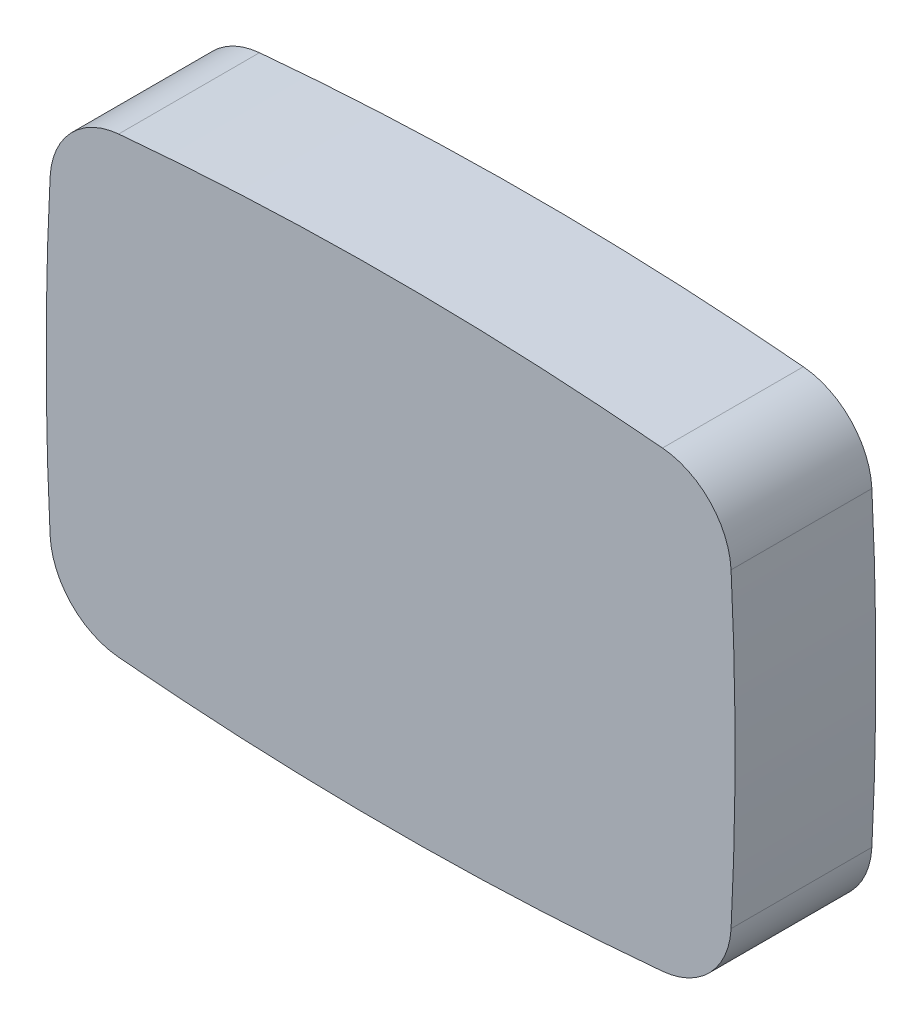
SolidWorks part; units mm, degrees
material "AW5083 AlMg4,5Mn"
ref_plane "Ebene vorne" through (0, 0, 0) normal (0, 0, 1) x (1, 0, 0)
ref_plane "Ebene oben" through (0, 0, 0) normal (0, 1, 0) x (1, 0, 0)
ref_plane "Ebene rechts" through (0, 0, 0) normal (1, 0, 0) x (0, 0, -1)
sketch "Skizze2" plane through (0, 0, 0) normal (0, 0, 1) x (1, 0, 0)
  line L1 (-68.5, 47.5) -> (68.5, 47.5) construction
  line L2 (-68.5, 47.5) -> (-68.5, -47.5) construction
  line L3 (-68.5, -47.5) -> (68.5, -47.5) construction
  line L4 (68.5, 47.5) -> (68.5, -47.5) construction
  line L5 (0, -47.5) -> (0, 47.5) construction
  line L6 (-68.5, 0) -> (68.5, 0) construction
  arc A0 (54.076, 45.0582) -> (-54.076, 45.0582) centre (0, -552.5) ccw
  arc A1 (-67.7042, 30.8915) -> (-67.7042, -30.8915) centre (531.5, 0) ccw
  arc A2 (-54.076, 45.0582) -> (-67.7042, 30.8915) centre (-52.7241, 30.1192) ccw
  arc A3 (67.7042, 30.8915) -> (67.7042, -30.8915) centre (-531.5, 0) cw
  arc A4 (54.076, 45.0582) -> (67.7042, 30.8915) centre (52.7241, 30.1192) cw
  arc A5 (54.076, -45.0582) -> (67.7042, -30.8915) centre (52.7241, -30.1192) ccw
  arc A6 (54.076, -45.0582) -> (-54.076, -45.0582) centre (0, 552.5) cw
  arc A7 (-54.076, -45.0582) -> (-67.7042, -30.8915) centre (-52.7241, -30.1192) cw
  point P0 (0, 0)
  dimension "D3" = 600
  dimension "D4" = 600
  dimension "D5" = 15
  dimension "D1" = 137
  dimension "D2" = 95
extrude "Grundform" add sketch "Skizze2" along normal blind 28
sketch "Mittellinien" plane through (0, 0, 0) normal (0, 0, -1) x (-1, 0, 0)
  line L0 (-63.5342, 40.5184) -> (0, 0) construction
  line L1 (0, 0) -> (-68.5, 0) construction
  line L2 (0, 0) -> (63.5342, -40.5184) construction
  line L3 (0, 0) -> (-63.5342, -40.5184) construction
  line L4 (63.5342, 40.5184) -> (0, 0) construction
  arc A0 (-67.7042, 30.8915) -> (-67.7042, -30.8915) centre (531.5, 0) ccw construction
  arc A1 (-67.7042, -30.8915) -> (-54.076, -45.0582) centre (-52.7241, -30.1192) ccw construction
  arc A2 (-54.076, 45.0582) -> (-67.7042, 30.8915) centre (-52.7241, 30.1192) ccw construction
  arc A3 (54.076, -45.0582) -> (67.7042, -30.8915) centre (52.7241, -30.1192) ccw construction
  arc A4 (67.7042, 30.8915) -> (54.076, 45.0582) centre (52.7241, 30.1192) ccw construction
  dimension "D1" = 68.5
  dimension "D4" = 75.3547
  dimension "D8" = 32.527
sketch "Radius lang 1" plane through (0, 0, 0) normal (0, 1, 0) x (1, 0, 0)
  line L0 (-54.076, -28) -> (54.076, -28) construction
  line L2 (0, 0) -> (0, 20)
  line L3 (54.076, 0) -> (-54.076, 0) construction
  line L4 (68.5, 0) -> (0, 0)
  arc A0 (68.5, 0) -> (0, 20) centre (0, -107.3063) ccw
  dimension "D1" = 48
  dimension "D2" = 127.3063
sketch "Seite 2" plane through (0, 0, 0) normal (1, 0, 0) x (0, 0, -1)
  line L0 (0, 0) -> (0, -47.5)
  line L1 (20, 0) -> (0, 0)
  arc A1 (17.8273, -16) -> (20, 0) centre (-40, 0) ccw
  arc A2 (0, -47.5) -> (17.8273, -16) centre (-54.0615, 3.8906) ccw
  dimension "D1" = 60
  dimension "D4" = 74.5899
  dimension "D2" = 20
  dimension "D3" = 16
ref_plane "Ebene2" through (0, -14.0128, -19.2722) normal (0, -0.5881, -0.8088) x (-1, 0, 0)
sketch "Schraeg1" plane through (0, -14.0128, -19.2722) normal (0, -0.5881, -0.8088) x (-1, 0, 0)
  line L1 (0, -32.7714) -> (63.5342, -32.7714)
  line L2 (0, -2.4569) -> (0, -32.7714)
  line L3 (0, -32.7714) -> (-63.5342, -32.7714) construction
  arc A0 (0, -2.4569) -> (63.5342, -32.7714) centre (0, -84.1928) cw
  arc A1 (0, -2.4569) -> (-63.5342, -32.7714) centre (0, -84.1928) ccw construction
sketch "Radius lang 2" plane through (0, 0, 0) normal (0, 1, 0) x (1, 0, 0)
  line L0 (0, 0) -> (0, 20) construction
  line L1 (0, 0) -> (0, 20)
  line L2 (-68.5, 0) -> (0, 0)
  arc A0 (0, 20) -> (-68.5, 0) centre (0, -107.3063) ccw
  arc A1 (68.5, 0) -> (0, 20) centre (0, -107.3063) ccw construction
sketch "Skizze36" plane through (0, 0, 0) normal (1, 0, 0) x (0, 0, -1)
  line L0 (0, 0) -> (20, 0) construction
  line L1 (0, 0) -> (20, 0)
  line L2 (0, 40.5184) -> (0, 0) construction
  line L3 (0, 47.5) -> (0, 0)
  arc A0 (20, 0) -> (17.8273, 16) centre (-40, 0) ccw
  arc A1 (17.8273, -16) -> (20, 0) centre (-40, 0) ccw construction
  arc A2 (17.8273, 16) -> (0, 47.5) centre (-54.0615, -3.8906) ccw
  arc A3 (0, -47.5) -> (17.8273, -16) centre (-54.0615, 3.8906) ccw construction
ref_plane "Ebene3" through (0, 14.0128, -19.2722) normal (0, 0.5881, -0.8088) x (-1, 0, 0)
sketch "Scharaeg2" plane through (0, 14.0128, -19.2722) normal (0, 0.5881, -0.8088) x (-1, 0, 0)
  line L0 (63.5342, 32.7714) -> (0, 32.7714)
  line L1 (0, 2.4569) -> (0, 32.7714)
  line L2 (0, 32.7714) -> (-63.5342, 32.7714) construction
  arc A0 (63.5342, 32.7714) -> (0, 2.4569) centre (0, 84.1928) cw
  arc A1 (0, 2.4569) -> (-63.5342, 32.7714) centre (0, 84.1928) cw construction
sketch "Skizze38" plane through (0, 0, 0) normal (0, 0, -1) x (-1, 0, 0)
  line L0 (68.5, 0) -> (0, 0) construction
  line L1 (0, 0) -> (63.5342, 40.5184) construction
  line L2 (68.5, 0) -> (0, 0) construction
  line L3 (68.5, 0) -> (0, 0) construction
  line L4 (0, 0) -> (63.5342, -40.5184) construction
  arc A0 (67.7042, 30.8915) -> (54.076, 45.0582) centre (52.7241, 30.1192) ccw construction
  arc A2 (67.7042, 30.8915) -> (63.5342, 40.5184) centre (52.7241, 30.1192) ccw
  arc A3 (67.7042, -30.8915) -> (67.7042, 30.8915) centre (-531.5, 0) ccw construction
  arc A4 (67.7042, -30.8915) -> (67.7042, 30.8915) centre (-531.5, 0) ccw
  arc A5 (54.076, -45.0582) -> (67.7042, -30.8915) centre (52.7241, -30.1192) ccw construction
  arc A6 (63.5342, -40.5184) -> (67.7042, -30.8915) centre (52.7241, -30.1192) ccw
